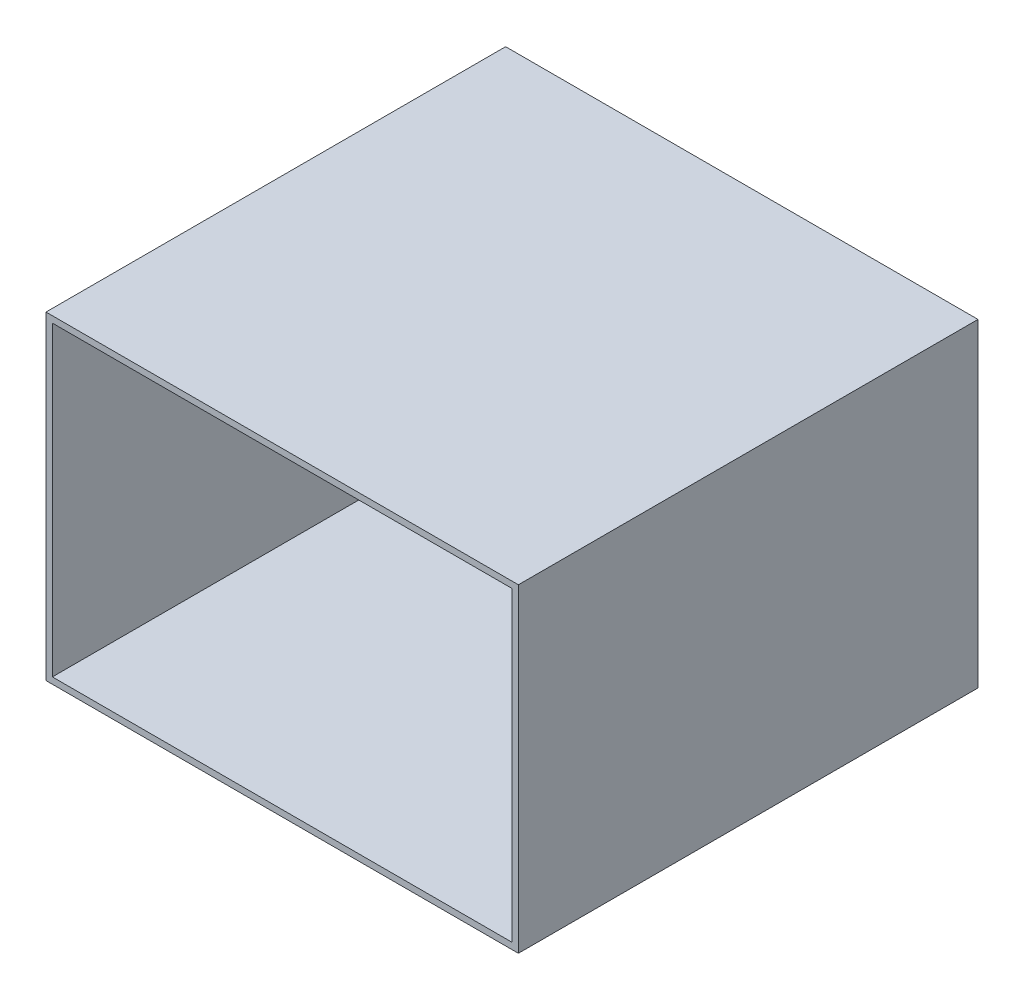
SolidWorks part; units mm, degrees
material "Acrylic (Medium-high impact)"
ref_plane "Front Plane" through (0, 0, 0) normal (0, 0, 1) x (1, 0, 0)
ref_plane "Top Plane" through (0, 0, 0) normal (0, 1, 0) x (1, 0, 0)
ref_plane "Right Plane" through (0, 0, 0) normal (1, 0, 0) x (0, 0, -1)
sketch "Sketch1" plane through (0, 0, 0) normal (0, 0, 1) x (1, 0, 0)
  line L0 (0, 152.4) -> (457.2, 152.4) construction
  line L1 (0, 0) -> (457.2, 0)
  line L2 (0, 0) -> (0, 304.8)
  line L3 (0, 304.8) -> (457.2, 304.8)
  line L4 (457.2, 0) -> (457.2, 304.8)
  line L5 (228.6, 304.8) -> (228.6, 0) construction
  circle A0 centre (228.6, 152.4) radius 25.4
  dimension "D3" = 50.8
  dimension "D1" = 457.2
  dimension "D2" = 304.8
extrude "Chamber Base" add sketch "Sketch1" along normal blind 6.35
sketch "Sketch2" plane through (457.2, 0, 0) normal (1, 0, 0) x (0, 0, -1)
  line L1 (0, 0) -> (-457.2, 0)
  line L2 (0, 0) -> (0, 304.8)
  line L3 (0, 304.8) -> (-457.2, 304.8)
  line L4 (-457.2, 0) -> (-457.2, 304.8)
  dimension "D1" = 304.8
  dimension "D2" = 457.2
extrude "Back wall" add sketch "Sketch2" along normal blind 6.35
sketch "Sketch3" plane through (0, 304.8, 0) normal (0, 1, 0) x (1, 0, 0)
  line L0 (463.55, 0) -> (463.55, -457.2) construction
  line L1 (0, 0) -> (463.55, 0)
  line L2 (0, 0) -> (0, -457.2)
  line L3 (0, -457.2) -> (463.55, -457.2)
  line L4 (463.55, 0) -> (463.55, -457.2)
  dimension "D1" = 457.2
extrude "Side wall 2" add sketch "Sketch3" along normal blind 6.35
sketch "Sketch5" plane through (0, 0, 0) normal (0, -1, 0) x (1, 0, 0)
  line L0 (463.55, 457.2) -> (463.55, 0) construction
  line L1 (0, 0) -> (463.55, 0)
  line L2 (0, 0) -> (0, 457.2)
  line L3 (0, 457.2) -> (463.55, 457.2)
  line L4 (463.55, 0) -> (463.55, 457.2)
  dimension "D1" = 457.2
extrude "Side wall 3" add sketch "Sketch5" along normal blind 6.35
sketch "Sketch6" plane through (0, 0, 0) normal (-1, 0, 0) x (0, 0, 1)
  line L1 (0, 311.15) -> (457.2, 311.15)
  line L2 (0, 311.15) -> (0, -6.35)
  line L3 (0, -6.35) -> (457.2, -6.35)
  line L4 (457.2, 311.15) -> (457.2, -6.35)
extrude "Boss-Extrude1" add sketch "Sketch6" along normal blind 6.35
sketch "Sketch7" plane through (0, 0, 0) normal (0, 0, -1) x (-1, 0, 0)
  line L0 (0, 0) -> (0, 304.8) construction
  line L1 (-429.735, 279.4) -> (-421.165, 279.4)
  line L2 (-431.8, 277.335) -> (-431.8, 268.765)
  line L3 (-429.735, 266.7) -> (-421.165, 266.7)
  line L4 (-419.1, 277.335) -> (-419.1, 268.765)
  line L5 (0, 304.8) -> (-457.2, 304.8) construction
  line L6 (-457.2, 304.8) -> (-457.2, 0) construction
  line L7 (0, 0) -> (-457.2, 0) construction
  line L8 (-228.6, 304.8) -> (-228.6, 0) construction
  line L9 (-457.2, 152.4) -> (0, 152.4) construction
  line L10 (-38.1, 277.335) -> (-38.1, 268.765)
  line L11 (-27.465, 266.7) -> (-36.035, 266.7)
  line L12 (-25.4, 277.335) -> (-25.4, 268.765)
  line L13 (-27.465, 279.4) -> (-36.035, 279.4)
  line L14 (-27.465, 25.4) -> (-36.035, 25.4)
  line L15 (-25.4, 27.465) -> (-25.4, 36.035)
  line L16 (-27.465, 38.1) -> (-36.035, 38.1)
  line L17 (-38.1, 27.465) -> (-38.1, 36.035)
  line L18 (-419.1, 27.465) -> (-419.1, 36.035)
  line L19 (-429.735, 38.1) -> (-421.165, 38.1)
  line L20 (-431.8, 27.465) -> (-431.8, 36.035)
  line L21 (-429.735, 25.4) -> (-421.165, 25.4)
  arc A0 (-419.1, 277.335) -> (-421.165, 279.4) centre (-421.165, 277.335) ccw
  arc A1 (-431.8, 277.335) -> (-429.735, 279.4) centre (-429.735, 277.335) cw
  arc A2 (-429.735, 266.7) -> (-431.8, 268.765) centre (-429.735, 268.765) cw
  arc A3 (-421.165, 266.7) -> (-419.1, 268.765) centre (-421.165, 268.765) ccw
  arc A4 (-36.035, 266.7) -> (-38.1, 268.765) centre (-36.035, 268.765) cw
  arc A5 (-27.465, 266.7) -> (-25.4, 268.765) centre (-27.465, 268.765) ccw
  arc A6 (-25.4, 277.335) -> (-27.465, 279.4) centre (-27.465, 277.335) ccw
  arc A7 (-38.1, 277.335) -> (-36.035, 279.4) centre (-36.035, 277.335) cw
  arc A8 (-38.1, 27.465) -> (-36.035, 25.4) centre (-36.035, 27.465) ccw
  arc A9 (-25.4, 27.465) -> (-27.465, 25.4) centre (-27.465, 27.465) cw
  arc A10 (-27.465, 38.1) -> (-25.4, 36.035) centre (-27.465, 36.035) cw
  arc A11 (-36.035, 38.1) -> (-38.1, 36.035) centre (-36.035, 36.035) ccw
  arc A12 (-421.165, 38.1) -> (-419.1, 36.035) centre (-421.165, 36.035) cw
  arc A13 (-429.735, 38.1) -> (-431.8, 36.035) centre (-429.735, 36.035) ccw
  arc A14 (-431.8, 27.465) -> (-429.735, 25.4) centre (-429.735, 27.465) ccw
  arc A15 (-419.1, 27.465) -> (-421.165, 25.4) centre (-421.165, 27.465) cw
  point P6 (-419.1, 279.4)
  point P13 (-419.1, 266.7)
  point P35 (-38.1, 266.7)
  point P36 (-38.1, 279.4)
  point P49 (-38.1, 25.4)
  point P50 (-38.1, 38.1)
  point P63 (-419.1, 38.1)
  point P64 (-419.1, 25.4)
  dimension "D2" = 2.065
  dimension "D3" = 2.065
  dimension "D4" = 2.065
  dimension "D5" = 2.065
  dimension "D1" = 12.7
  dimension "D6" = 304.8
  dimension "D7" = 457.2
  dimension "D8" = 25.4
  dimension "D9" = 25.4
extrude "Cut-Extrude1" cut sketch "Sketch7" against normal up to surface (6.35 mm away) up to face at (228.6, 152.4, 6.35)
